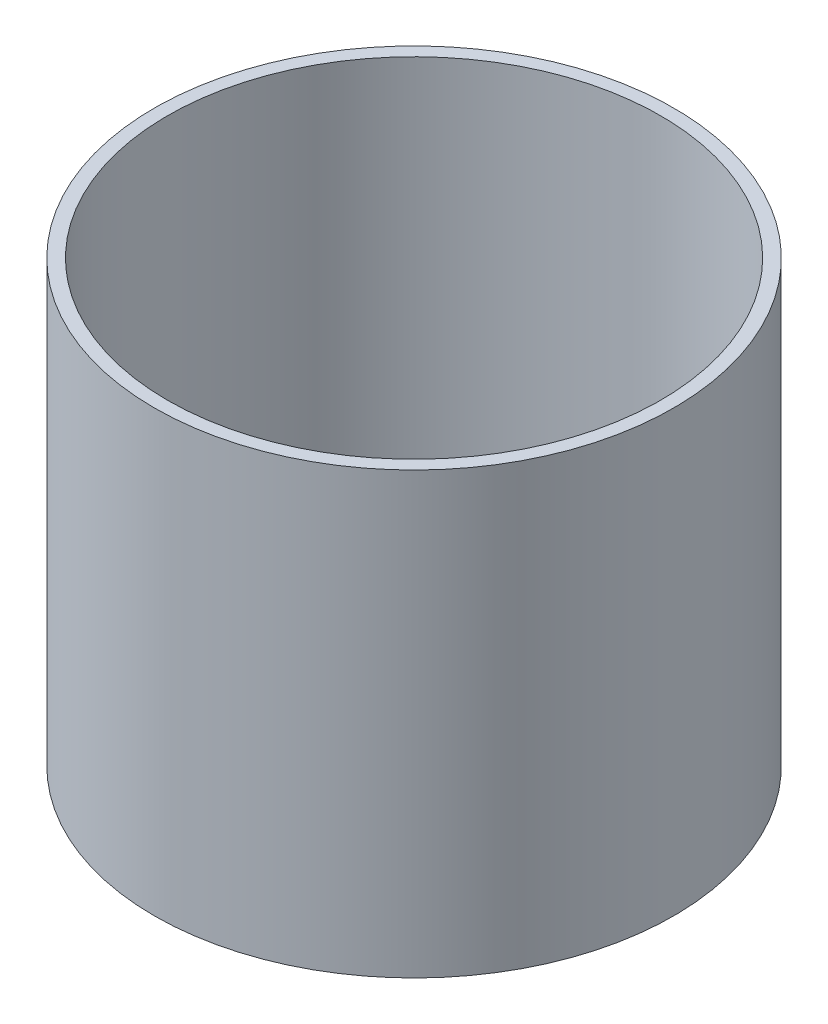
SolidWorks part; units mm, degrees
material "PVC Rigid"
ref_plane "Front Plane" through (0, 0, 0) normal (0, 0, 1) x (1, 0, 0)
ref_plane "Top Plane" through (0, 0, 0) normal (0, 1, 0) x (1, 0, 0)
ref_plane "Right Plane" through (0, 0, 0) normal (1, 0, 0) x (0, 0, -1)
sketch "Sketch1" plane through (0, 0, 0) normal (0, 1, 0) x (1, 0, 0)
  circle A0 centre (0, 0) radius 93.6625
  circle A1 centre (0, 0) radius 88.9
  dimension "D1" = 187.325
  dimension "D2" = 177.8
extrude "Boss-Extrude1" add sketch "Sketch1" along normal mid plane 158.6433
